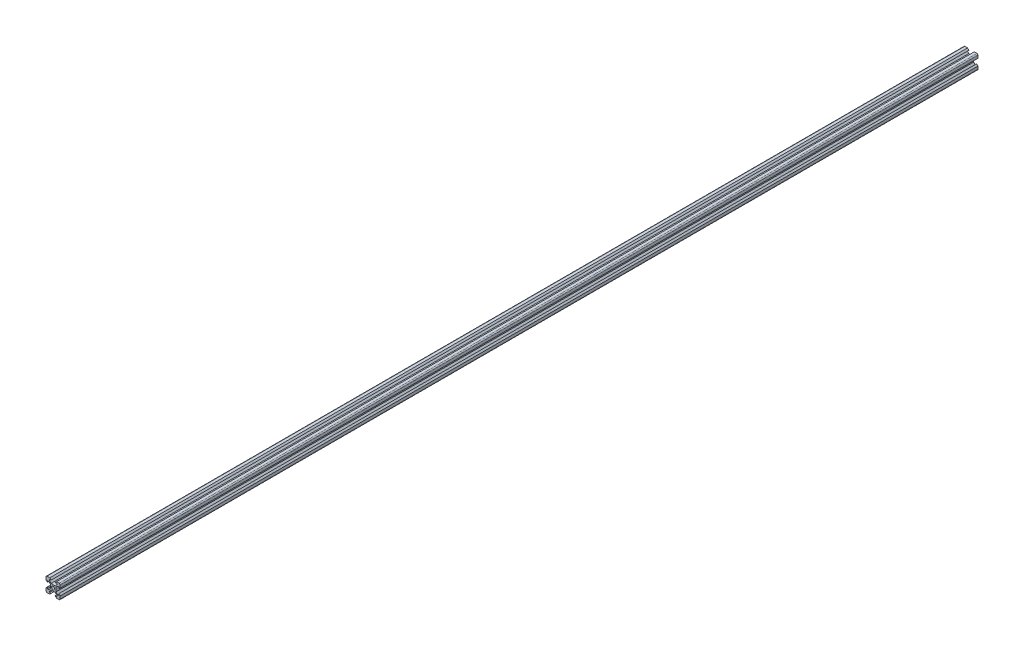
SolidWorks part; units mm, degrees
material "6061 Alloy"
ref_plane "Front Plane" through (0, 0, 0) normal (0, 0, 1) x (1, 0, 0)
ref_plane "Top Plane" through (0, 0, 0) normal (0, 1, 0) x (1, 0, 0)
ref_plane "Right Plane" through (0, 0, 0) normal (1, 0, 0) x (0, 0, -1)
sketch "Sketch1" plane through (0, 0, 0) normal (0, 0, 1) x (1, 0, 0)
  line L0 (15.6876, 55.3211) -> (115.0437, 55.3211) construction
  line L1 (8.1, 5.225) -> (8.1, 2.85)
  line L2 (-8.5, 10) -> (-4.75, 10)
  line L3 (-10, 8.5) -> (-10, 4.75)
  line L4 (-8.5, -10) -> (-4.75, -10)
  line L5 (10, 8.5) -> (10, 4.75)
  line L6 (6.325, 5.225) -> (4, 2.9)
  line L7 (-8.1, -2.85) -> (-8.1, -5.225)
  line L8 (-2.9, 4) -> (2.9, 4)
  line L9 (-4, 2.9) -> (-4, -2.9)
  line L10 (-2.9, -4) -> (2.9, -4)
  line L11 (4, 2.9) -> (4, -2.9)
  line L12 (2.85, -8.1) -> (5.225, -8.1)
  line L13 (-5.225, -8.1) -> (-2.85, -8.1)
  line L14 (5.225, 6.325) -> (2.9, 4)
  line L17 (-10, 4.75) -> (-8.1, 2.85)
  line L20 (4.75, -10) -> (8.5, -10)
  line L22 (-10, -4.75) -> (-10, -8.5)
  line L23 (10, -4.75) -> (10, -8.5)
  line L24 (-10, -4.75) -> (-8.1, -2.85)
  line L25 (-4.75, -10) -> (-2.85, -8.1)
  line L26 (4.75, -10) -> (2.85, -8.1)
  line L27 (10, -4.75) -> (8.1, -2.85)
  line L28 (10, 4.75) -> (8.1, 2.85)
  line L29 (-4.75, 10) -> (-2.85, 8.1)
  line L30 (4.75, 10) -> (2.85, 8.1)
  line L31 (8.1, -2.85) -> (8.1, -5.225)
  line L32 (6.325, -5.225) -> (8.1, -5.225)
  line L33 (5.225, -6.325) -> (5.225, -8.1)
  line L34 (4.75, 10) -> (8.5, 10)
  line L35 (2.85, 8.1) -> (5.225, 8.1)
  line L36 (10, -10) -> (10.975, -10.975) construction
  line L37 (-5.225, 8.1) -> (-2.85, 8.1)
  line L38 (-8.1, -5.225) -> (-6.325, -5.225)
  line L39 (-5.225, 6.325) -> (-2.9, 4)
  line L40 (-8.1, 5.225) -> (-8.1, 2.85)
  line L41 (-5.225, -6.325) -> (-5.225, -8.1)
  line L42 (-6.325, 5.225) -> (-4, 2.9)
  line L46 (-8.1, 5.225) -> (-6.325, 5.225)
  line L47 (-5.225, 8.1) -> (-5.225, 6.325)
  line L52 (8.1, 5.225) -> (6.325, 5.225)
  line L53 (5.225, 8.1) -> (5.225, 6.325)
  line L63 (4, -2.9) -> (6.325, -5.225)
  line L66 (2.9, -4) -> (5.225, -6.325)
  line L67 (-2.9, -4) -> (-5.225, -6.325)
  line L70 (-4, -2.9) -> (-6.325, -5.225)
  arc A0 (-8.5, -10) -> (-10, -8.5) centre (-8.5, -8.5) cw
  arc A1 (8.5, -10) -> (10, -8.5) centre (8.5, -8.5) ccw
  arc A2 (10, 8.5) -> (8.5, 10) centre (8.5, 8.5) ccw
  arc A3 (-8.5, 10) -> (-10, 8.5) centre (-8.5, 8.5) ccw
  circle A4 centre (0, 0) radius 2.125
  point P2 (0, 0)
  point P8 (0, 0)
  point P14 (-10, -10)
  point P20 (0, 0)
  point P49 (10, 10)
  point P52 (-10, 10)
extrude "Boss-Extrude1" add sketch "Sketch1" along normal blind 1292.4
